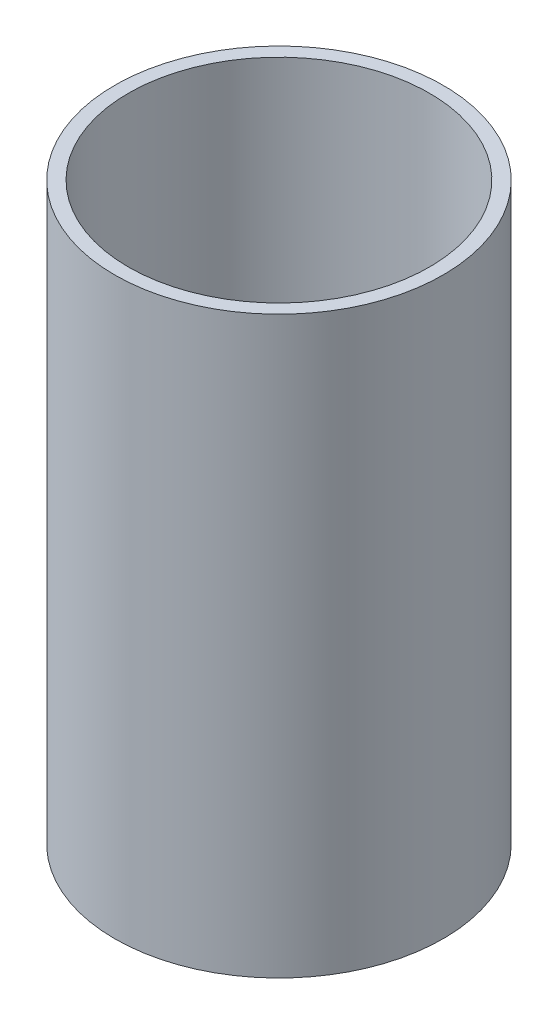
SolidWorks part; units mm, degrees
ref_plane "Front Plane" through (0, 0, 0) normal (0, 0, 1) x (1, 0, 0)
ref_plane "Top Plane" through (0, 0, 0) normal (0, 1, 0) x (1, 0, 0)
ref_plane "Right Plane" through (0, 0, 0) normal (1, 0, 0) x (0, 0, -1)
sketch "Sketch1" plane through (0, 0, 0) normal (0, 1, 0) x (1, 0, 0)
  circle A0 centre (0, 0) radius 11
  circle A1 centre (0, 0) radius 12
  dimension "D1" = 22
  dimension "D2" = 24
extrude "Boss-Extrude1" add sketch "Sketch1" along normal mid plane 42
